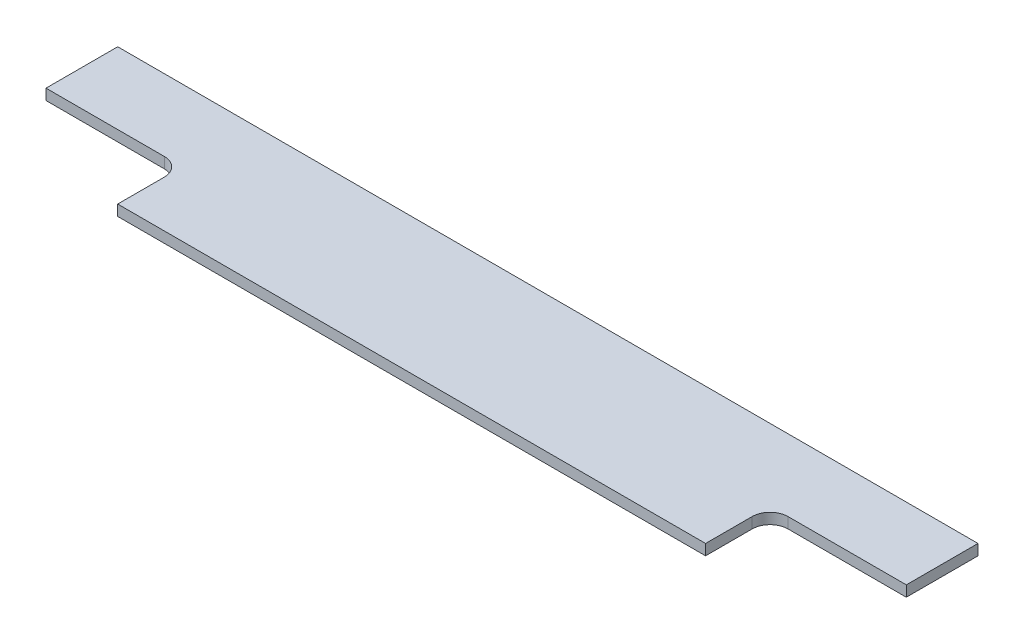
SolidWorks part; units mm, degrees
ref_plane "Front Plane" through (0, 0, 0) normal (0, 0, 1) x (1, 0, 0)
ref_plane "Top Plane" through (0, 0, 0) normal (0, 1, 0) x (1, 0, 0)
ref_plane "Right Plane" through (0, 0, 0) normal (1, 0, 0) x (0, 0, -1)
sketch "Sketch1" plane through (0, 0, 0) normal (0, 1, 0) x (1, 0, 0)
  line L1 (-120, 19) -> (120, 19)
  line L2 (-120, 19) -> (-120, -19)
  line L3 (-120, -19) -> (120, -19)
  line L4 (120, 19) -> (120, -19)
  line L5 (0, -19) -> (0, 19) construction
  line L6 (-120, 0) -> (120, 0) construction
  point P0 (0, 0)
  dimension "D1" = 240
  dimension "D2" = 38
extrude "Boss-Extrude1" add sketch "Sketch1" along normal blind 3
sketch "Sketch2" plane through (0, 3, 0) normal (0, 1, 0) x (1, 0, 0)
  line L0 (0, 19) -> (0, -19) construction
  line L1 (-120, -19) -> (-82, -19)
  line L2 (-120, -19) -> (-120, -1)
  line L3 (-120, -1) -> (-82, -1)
  line L4 (-82, -19) -> (-82, -1)
  line L5 (-101, -1) -> (-101, -19) construction
  line L6 (-120, -10) -> (-82, -10) construction
  line L7 (120, 19) -> (-120, 19) construction
  line L8 (-120, -19) -> (120, -19) construction
  line L9 (120, -1) -> (82, -1)
  line L10 (82, -19) -> (82, -1)
  line L11 (120, -19) -> (82, -19)
  line L12 (120, -19) -> (120, -1)
  point P144 (-101, -10)
  dimension "D1" = 18
  dimension "D2" = 38
extrude "Cut-Extrude1" cut sketch "Sketch2" against normal blind 3
fillet "Fillet1" radius 5 2 edges at (82, 1.5, 1) (-82, 1.5, 1)
